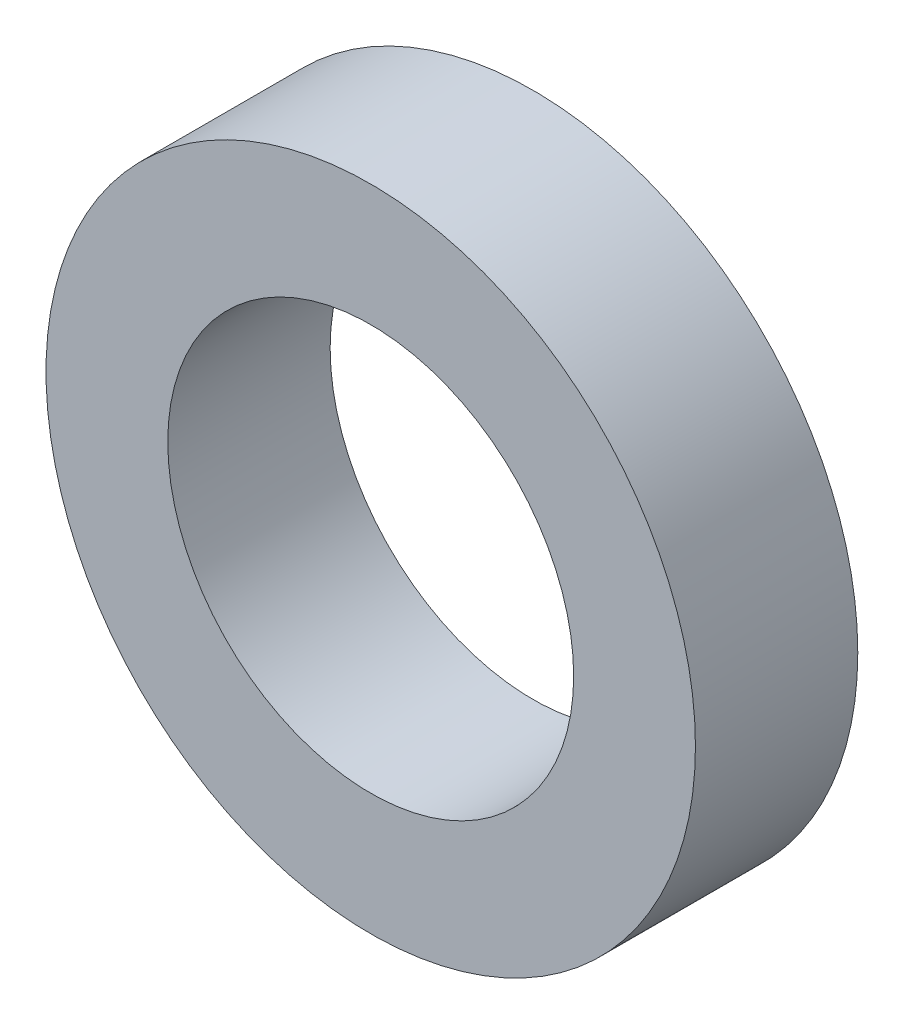
SolidWorks part; units mm, degrees
ref_plane "Front Plane" through (0, 0, 0) normal (0, 0, 1) x (1, 0, 0)
ref_plane "Top Plane" through (0, 0, 0) normal (0, 1, 0) x (1, 0, 0)
ref_plane "Right Plane" through (0, 0, 0) normal (1, 0, 0) x (0, 0, -1)
sketch "Sketch2" plane through (0, 0, 0) normal (0, 0, 1) x (1, 0, 0)
  circle A0 centre (0, 0) radius 2.5
  circle A1 centre (0, 0) radius 4
  dimension "D1" = 5
  dimension "D2" = 8
extrude "Boss-Extrude1" add sketch "Sketch2" along normal blind 2
